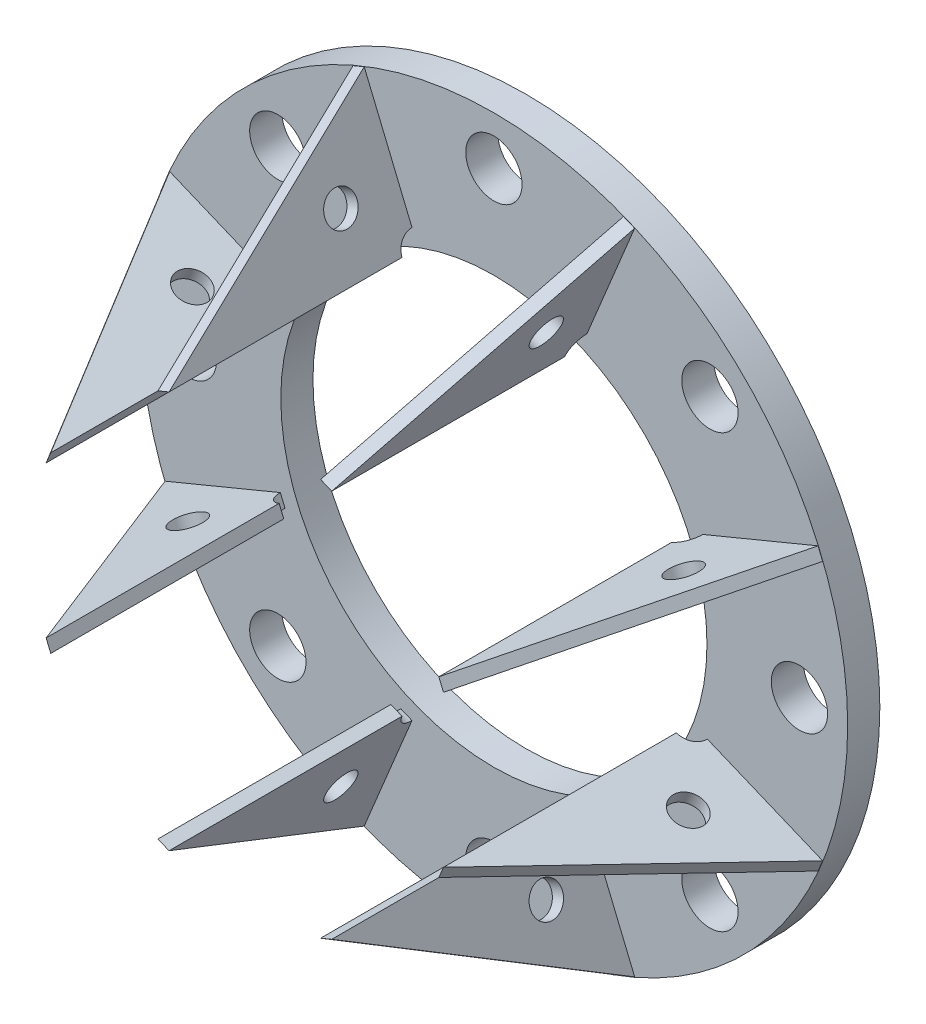
SolidWorks part; units mm, degrees
ref_plane "Front Plane" through (0, 0, 0) normal (0, 0, 1) x (1, 0, 0)
ref_plane "Top Plane" through (0, 0, 0) normal (0, 1, 0) x (1, 0, 0)
ref_plane "Right Plane" through (0, 0, 0) normal (1, 0, 0) x (0, 0, -1)
sketch "Sketch1" plane through (0, 0, 0) normal (0, 0, 1) x (1, 0, 0)
  circle A0 centre (0, 0) radius 84.1375
  circle A1 centre (0, 0) radius 139.7
  dimension "D1" = 168.275
  dimension "D2" = 279.4
extrude "Extrude1" add sketch "Sketch1" along normal blind 12.7
hole_wizard " (0.625) Diameter Hole1" positions "3DSketch1" profile "Sketch2" hole size "7/8" standard "Ansi Inch"
sketch3d "3DSketch1"
  line L10 (0, 139.7, 12.7) -> (0, 0, 12.7) construction
  circle A2 centre (0, 0, 12.7) radius 139.7 construction
  circle A3 centre (0, 0, 12.7) radius 139.7 construction
  point P5 (0, 120.65, 12.7)
  point P24 (0, 0, 152.4)
  point P26 (0, 0, 152.4)
  dimension "D1" = 120.65
sketch "Sketch2" plane through (0, 120.65, 12.7) normal (1, 0, 0) x (0, -1, 0)
  line L0 (0, 0) -> (0, 32.0771)
  line L1 (0, 32.0771) -> (11.1125, 25.4)
  line L2 (11.1125, 25.4) -> (11.1125, 0)
  line L5 (11.1125, 0) -> (0, 0)
  line L10 (0, 32.0771) -> (-11.1125, 25.4) construction
  line L11 (0, -6.35) -> (0, 107.95) construction
  dimension "Hole Dia." = 22.225
  dimension "Hole Depth" = 25.4
  dimension "Drill Angle" = 118
pattern_circular "CirPattern1" [suppressed] count 4 over 360
pattern_circular "CirPattern2" count 8 over 360 about axis through (0, 0, 0) along (0, 0, 1) of " (0.625) Diameter Hole1"
sketch "Sketch4" plane through (0, 0, 12.7) normal (0, 0, 1) x (1, 0, 0)
  line L0 (0, 0) -> (0, 139.7) construction
  line L1 (0, 0) -> (-139.7, 0) construction
  line L2 (-99.3557, 98.2066) -> (-60.066, 58.9168) construction
  line L3 (-99.9167, 89.7873) -> (-68.4853, 58.3559)
  line L4 (-99.9167, 89.7873) -> (-90.9364, 98.7675)
  line L5 (-68.4853, 58.3559) -> (-59.5051, 67.3362)
  line L6 (-90.9364, 98.7675) -> (-59.5051, 67.3362)
  line L7 (-99.9167, 89.7873) -> (-59.5051, 67.3362) construction
  line L8 (-68.4853, 58.3559) -> (-90.9364, 98.7675) construction
  circle A0 centre (0, 0) radius 139.7 construction
  circle A1 centre (0, 0) radius 84.1375 construction
  point P12 (-79.7109, 78.5617)
  dimension "D1" = 45
  dimension "D2" = 12.7
extrude "Extrude2" [suppressed] add sketch "Sketch4" along normal blind 55.5625
sketch "Sketch5" [suppressed] plane through (-4.7316, -4.7316, 0) normal (-0.7071, -0.7071, 0) x (0, 0, 1)
  line L0 (57.15, 44.4487) -> (57.15, 88.8993)
  line L1 (57.15, 88.8993) -> (12.7, 88.8993)
  line L2 (12.7, 88.8993) -> (57.15, 44.4487)
extrude "Extrude3" [suppressed] cut sketch "Sketch5" against normal through all
pattern_circular "CirPattern3" [suppressed] count 4 over 360
sketch "Sketch6" plane through (0, 0, 12.7) normal (0, 0, 1) x (1, 0, 0)
  line L0 (0, 0) -> (0, 139.7) construction
  line L1 (-55.5967, 127.9997) -> (-34.3132, 76.6169)
  line L2 (-53.4609, 129.066) -> (-32.049, 77.3732) construction
  line L3 (-55.5967, 127.9997) -> (-51.1967, 129.8223)
  line L4 (-34.3132, 76.6169) -> (-29.9132, 78.4394)
  line L5 (-51.1967, 129.8223) -> (-29.9132, 78.4394)
  line L6 (-55.5967, 127.9997) -> (-29.9132, 78.4394) construction
  line L7 (-34.3132, 76.6169) -> (-51.1967, 129.8223) construction
  line L8 (-32.049, 77.3732) -> (0, 0) construction
  circle A0 centre (0, 0) radius 139.7 construction
  point P9 (-42.755, 103.2196)
  dimension "D1" = 22.5
  dimension "D2" = 4.7625
extrude "Extrude4" add sketch "Sketch6" along normal blind 98.3456
sketch "Sketch8" plane through (2.2, 0.9113, 0) normal (0.9239, 0.3827, 0) x (0, 0, -1)
  line L0 (-12.7, 139.5323) -> (-111.0456, 83.9159)
  line L1 (-111.0456, 83.9159) -> (-111.0456, 139.5323)
  line L2 (-111.0456, 139.5323) -> (-12.7, 139.5323)
  line L3 (-12.7, 84.1038) -> (-12.7, 139.5323) construction
  line L4 (-111.0456, 83.9159) -> (-12.7, 83.9159) construction
  line L5 (-12.7, 90.2659) -> (-12.7, 83.9159)
  line L6 (-12.7, 83.9159) -> (-19.05, 83.9159)
  line L7 (-12.7, 83.9159) -> (-17.1901, 88.406) construction
  line L8 (-17.1901, 88.406) -> (-48.2258, 119.4417) construction
  circle A0 centre (-34.7554, 105.9713) radius 6.35
  arc A1 (-12.7, 90.2659) -> (-19.05, 83.9159) centre (-12.7, 83.9159) ccw
  dimension "D1" = 6.35
  dimension "D2" = 19.05
extrude "Extrude5" cut sketch "Sketch8" against normal up to next (4.7625 mm away)
pattern_circular "CirPattern4" count 8 over 360 about axis through (0, 0, 0) along (0, 0, 1) of "Extrude4", "Extrude5"
equation "\"D1@Extrude2\" = (\"D2@Sketch1\" - \"D1@Sketch1\")/2"
equation "\"D1@Extrude4\" = (\"D2@Sketch1\" - \"D1@Sketch1\") / 2 * 1.77"
